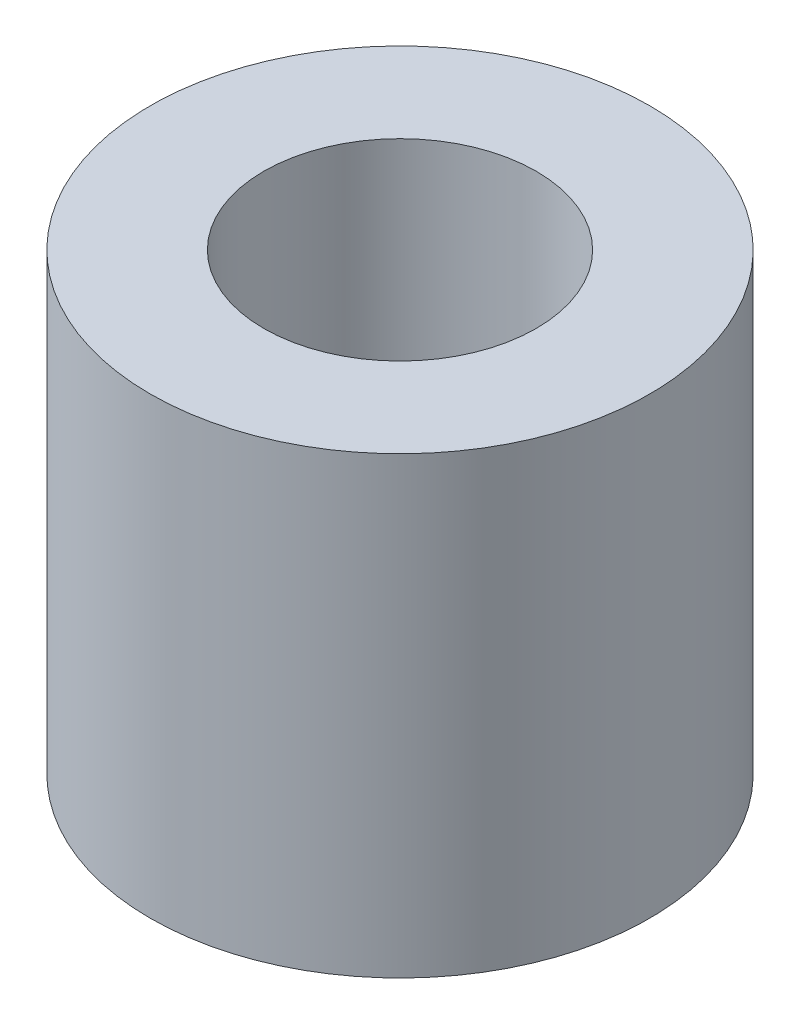
SolidWorks part; units mm, degrees
material "PMMA"
ref_plane "Front" through (0, 0, 0) normal (0, 0, 1) x (1, 0, 0)
ref_plane "Top" through (0, 0, 0) normal (0, 1, 0) x (1, 0, 0)
ref_plane "Right" through (0, 0, 0) normal (1, 0, 0) x (0, 0, -1)
sketch "Эскиз1" plane through (0, 0, 0) normal (0, 1, 0) x (1, 0, 0)
  circle A0 centre (0, 0) radius 1.5
  circle A1 centre (0, 0) radius 2.75
  dimension "D1" = 5.5
  dimension "D2" = 3
extrude "Бобышка-Вытянуть1" add sketch "Эскиз1" along normal blind 5
